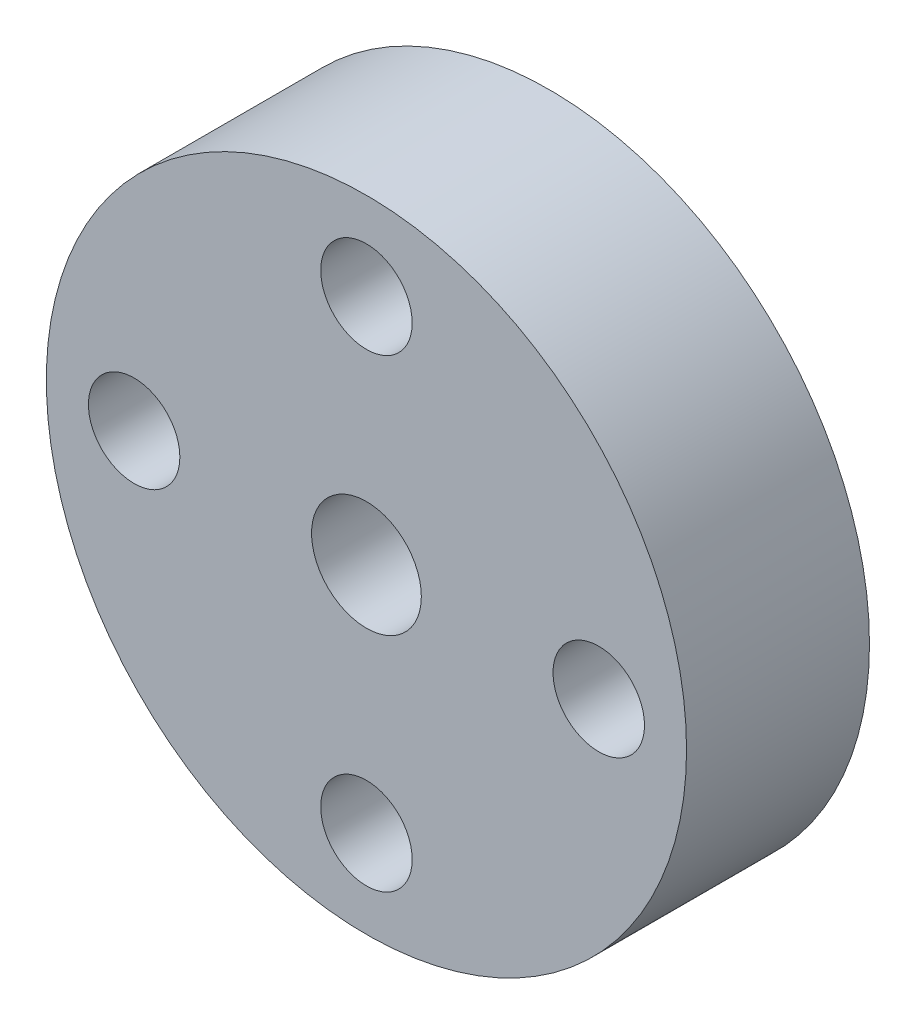
SolidWorks part; units mm, degrees
ref_plane "정면" through (0, 0, 0) normal (0, 0, 1) x (1, 0, 0)
ref_plane "윗면" through (0, 0, 0) normal (0, 1, 0) x (1, 0, 0)
ref_plane "우측면" through (0, 0, 0) normal (1, 0, 0) x (0, 0, -1)
sketch "스케치1" plane through (0, 0, 0) normal (0, 0, 1) x (1, 0, 0)
  circle A0 centre (0, 0) radius 8.75
  dimension "D1" = 17.5
extrude "보스-돌출1" add sketch "스케치1" along normal blind 5
hole_wizard "M3 나사 구멍1" positions "스케치2" profile "스케치3" tap size "M3" standard "ISO" end condition up to next
sketch "스케치2" plane through (0, 0, 5) normal (0, 0, 1) x (1, 0, 0)
  line L0 (0, 0) -> (5.2284, 0) construction
  point P0 (0, 6.35)
  point P15 (6.35, 0)
  point P16 (0, -6.35)
  point P17 (-6.35, 0)
  dimension "D1" = 6.35
  dimension "D2" = 4
sketch "스케치3" plane through (0, 6.35, 5) normal (1, 0, 0) x (0, -1, 0)
  line L0 (0, 0) -> (0, 5)
  line L1 (0, 5) -> (1.25, 5)
  line L2 (1.25, 5) -> (1.25, 0)
  line L5 (1.25, 0) -> (0, 0)
  line L11 (0, -6.35) -> (0, 107.95) construction
  dimension "관통 탭 드릴 지름" = 2.5
  dimension "관통 탭 드릴 깊이" = 5
cosmetic thread "구멍 나사산1"
cosmetic thread "구멍 나사산2"
cosmetic thread "구멍 나사산3"
cosmetic thread "구멍 나사산4"
sketch "스케치4" plane through (0, 0, 5) normal (0, 0, 1) x (1, 0, 0)
  circle A0 centre (0, 0) radius 1.5
  dimension "D1" = 3
extrude "컷-돌출1" cut sketch "스케치4" against normal through all
